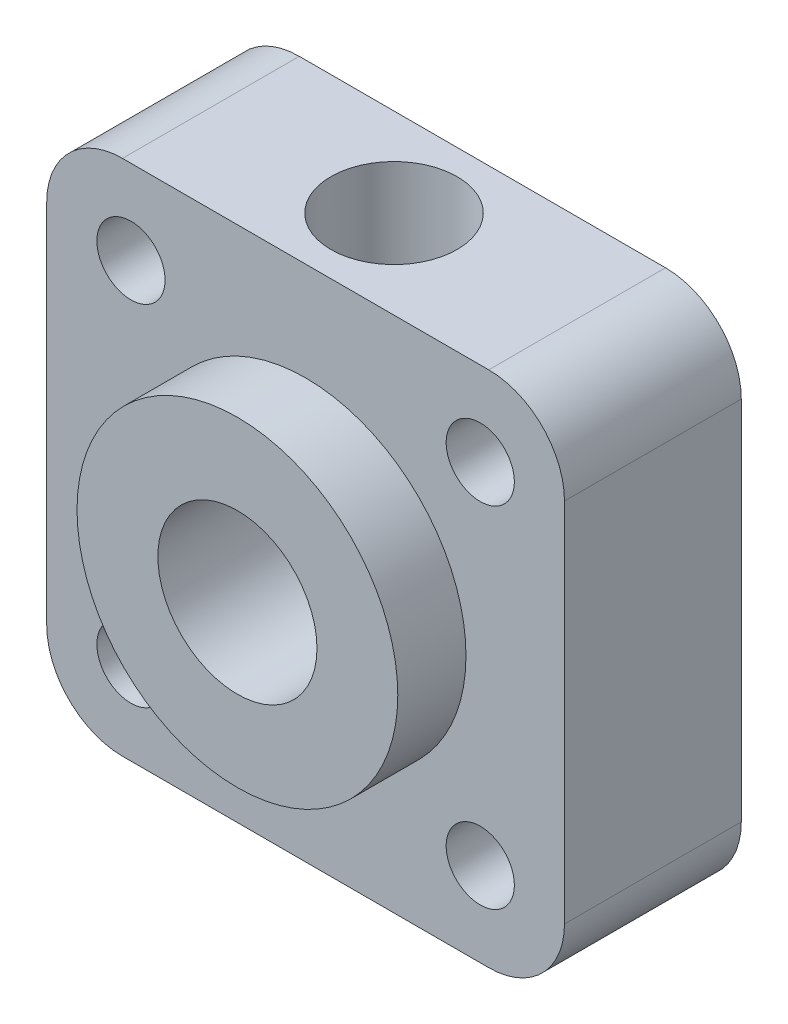
SolidWorks part; units mm, degrees
ref_plane "Alzado" through (0, 0, 0) normal (0, 0, 1) x (1, 0, 0)
ref_plane "Planta" through (0, 0, 0) normal (0, 1, 0) x (1, 0, 0)
ref_plane "Vista lateral" through (0, 0, 0) normal (1, 0, 0) x (0, 0, -1)
sketch "Croquis1" plane through (0, 0, 0) normal (0, 0, 1) x (1, 0, 0)
  line L1 (-10.25, 10.25) -> (10.25, 10.25)
  line L2 (-10.25, 10.25) -> (-10.25, -10.25)
  line L3 (-10.25, -10.25) -> (10.25, -10.25)
  line L4 (10.25, 10.25) -> (10.25, -10.25)
  line L5 (-10.25, 10.25) -> (10.25, -10.25) construction
  line L6 (-10.25, -10.25) -> (10.25, 10.25) construction
  point P0 (0, 0)
  dimension "D1" = 20.5
  dimension "D2" = 20.5
extrude "Saliente-Extruir1" add sketch "Croquis1" along normal blind 7
fillet "Redondeo1" radius 3 4 edges at (-10.25, -10.25, 3.5) (10.25, -10.25, 3.5) (10.25, 10.25, 3.5) (-10.25, 10.25, 3.5)
sketch "Croquis2" plane through (0, 0, 7) normal (0, 0, 1) x (1, 0, 0)
  circle A0 centre (0, 0) radius 6.35
  dimension "D1" = 12.7
extrude "Saliente-Extruir2" add sketch "Croquis2" along normal blind 2.7
sketch "Croquis3" plane through (0, 0, 9.7) normal (0, 0, 1) x (1, 0, 0)
  circle A0 centre (0, 0) radius 3.15
  dimension "D1" = 6.3
extrude "Cortar-Extruir1" cut sketch "Croquis3" against normal through all
sketch "Croquis4" plane through (0, 0, 7) normal (0, 0, 1) x (1, 0, 0)
  line L0 (-9.3713, 9.3713) -> (9.3713, -9.3713) construction
  line L1 (9.3713, 9.3713) -> (-9.3713, -9.3713) construction
  arc A0 (-7.25, 10.25) -> (-10.25, 7.25) centre (-7.25, 7.25) ccw construction
  arc A1 (7.25, -10.25) -> (10.25, -7.25) centre (7.25, -7.25) ccw construction
  arc A2 (10.25, 7.25) -> (7.25, 10.25) centre (7.25, 7.25) ccw construction
  arc A3 (-10.25, -7.25) -> (-7.25, -10.25) centre (-7.25, -7.25) ccw construction
  circle A4 centre (-6.9155, 6.9155) radius 1.35
  circle A5 centre (6.9155, 6.9155) radius 1.35
  circle A6 centre (6.9155, -6.9155) radius 1.35
  circle A7 centre (-6.9155, -6.9155) radius 1.35
  point P27 (1.8371, -2.5588)
  dimension "D1" = 2.7
  dimension "D2" = 2.7
  dimension "D3" = 2.7
  dimension "D4" = 2.7
  dimension "D5" = 9.78
  dimension "D6" = 9.78
  dimension "D7" = 9.78
  dimension "D8" = 9.78
extrude "Cortar-Extruir2" cut sketch "Croquis4" against normal through all
sketch "Croquis5" plane through (0, 10.25, 0) normal (0, 1, 0) x (1, 0, 0)
  line L0 (-7.25, 0) -> (7.25, -7) construction
  line L1 (-7.25, -7) -> (7.25, 0) construction
  circle A0 centre (0, -3.5) radius 2.5
  dimension "D1" = 5
extrude "Cortar-Extruir3" cut sketch "Croquis5" against normal up to next
